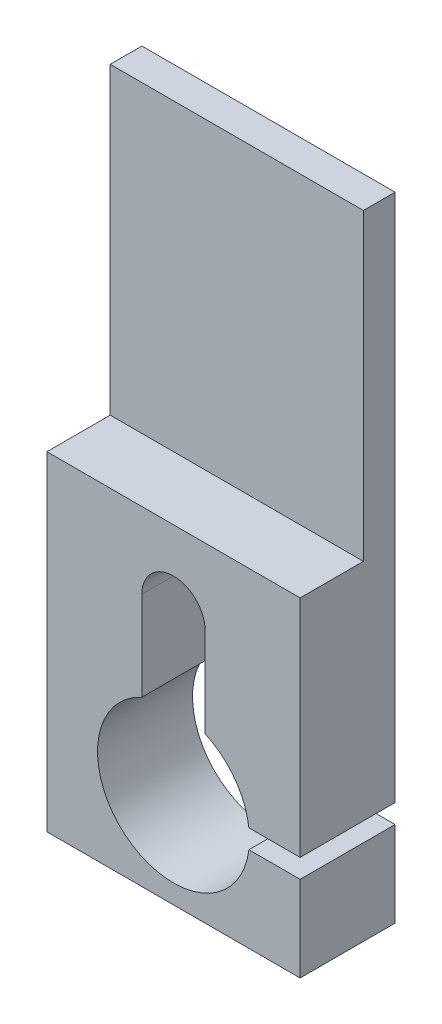
SolidWorks part; units mm, degrees
ref_plane "Plan de face" through (0, 0, 0) normal (0, 0, 1) x (1, 0, 0)
ref_plane "Plan de dessus" through (0, 0, 0) normal (0, 1, 0) x (1, 0, 0)
ref_plane "Plan de droite" through (0, 0, 0) normal (1, 0, 0) x (0, 0, -1)
sketch "Esquisse1" plane through (0, 0, 0) normal (0, 0, 1) x (1, 0, 0)
  line L0 (0, 0) -> (-40, 0)
  line L1 (-40, 0) -> (-40, 100)
  line L2 (0, 0) -> (0, 13.5)
  line L3 (-40, 100) -> (0, 100)
  line L4 (-20, 0) -> (-20, 45.3168) construction
  line L5 (-15, 25.9087) -> (-15, 40)
  line L6 (-25, 0) -> (-25, 45.3168) construction
  line L7 (-15, 0) -> (-15, 45.3168) construction
  line L8 (-25, 25.9087) -> (-25, 40)
  line L9 (0, 16.5) -> (0, 100)
  line L10 (-8.0941, 13.5) -> (0, 13.5)
  line L11 (-8.0941, 16.5) -> (0, 16.5)
  arc A0 (-8.0941, 16.5) -> (-15, 25.9087) centre (-20, 15) ccw
  arc A1 (-25, 25.9087) -> (-8.0941, 13.5) centre (-20, 15) ccw
  arc A2 (-15, 40) -> (-25, 40) centre (-20, 40) ccw
extrude "Extrusion1" add sketch "Esquisse1" along normal blind 15
sketch "Esquisse2" plane through (0, 0, 15) normal (0, 0, 1) x (1, 0, 0)
  line L0 (-40, 100) -> (0, 100)
  line L1 (0, 100) -> (0, 52)
  line L2 (0, 16.5) -> (0, 100) construction
  line L3 (0, 52) -> (-40, 52)
  line L4 (-40, 100) -> (-40, 0) construction
  line L5 (-40, 52) -> (-40, 100)
extrude "Extrusion2" cut sketch "Esquisse2" against normal blind 10
